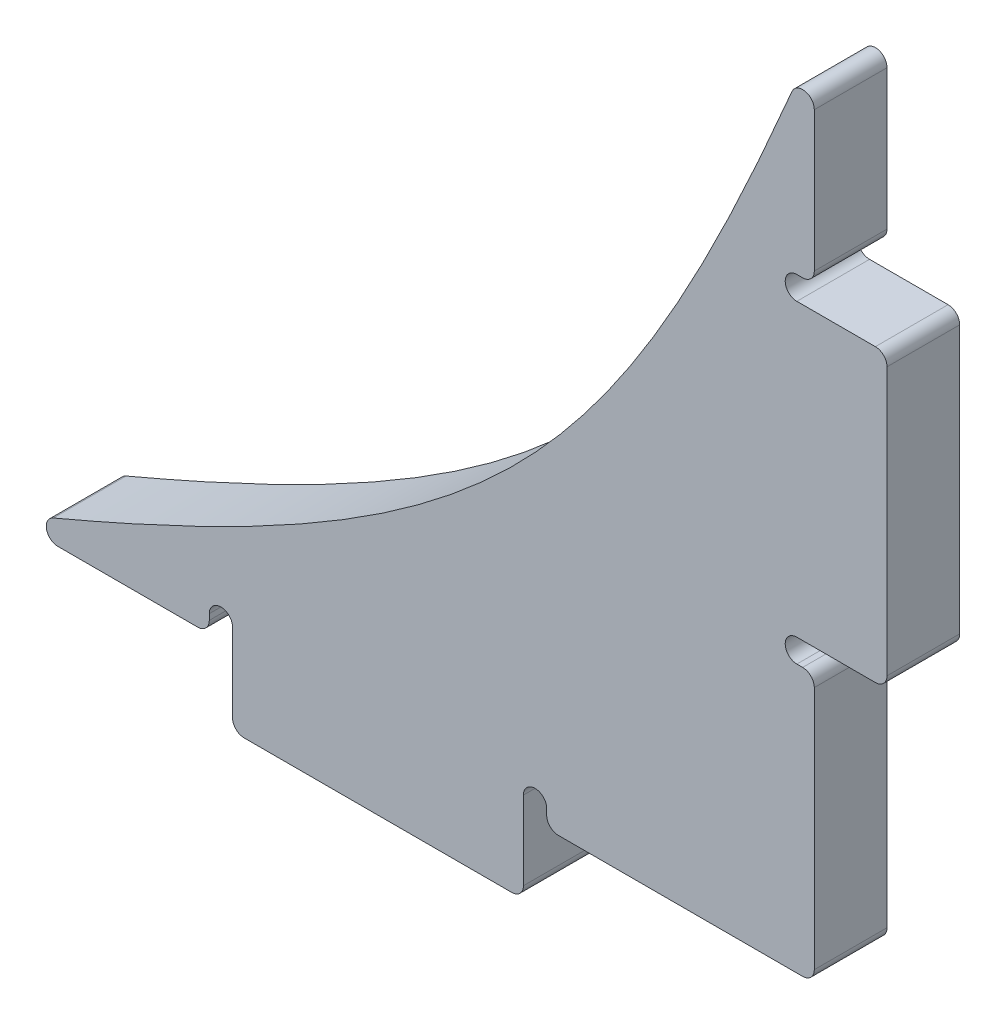
SolidWorks part; units mm, degrees
material "6061-T6 (SS)"
ref_plane "Front Plane" through (0, 0, 0) normal (0, 0, 1) x (1, 0, 0)
ref_plane "Top Plane" through (0, 0, 0) normal (0, 1, 0) x (1, 0, 0)
ref_plane "Right Plane" through (0, 0, 0) normal (1, 0, 0) x (0, 0, -1)
sketch "Sketch1" plane through (0, 0, 0) normal (0, 0, 1) x (1, 0, 0)
  line L0 (22.86, 22.86) -> (14.0603, 1.4879) construction
  line L1 (22.86, -12.7) -> (-12.7, -12.7)
  line L2 (22.86, -12.7) -> (22.86, 22.86)
  line L5 (5.08, 5.08) -> (22.86, -12.7) construction
  line L6 (22.86, 22.86) -> (-12.7, -12.7) construction
  line L7 (14.0603, 1.4879) -> (8.6721, -3.9003) construction
  line L8 (8.6721, -3.9003) -> (-12.7, -12.7) construction
  spline S0 degree 3 poles (22.86, 22.86) (14.0603, 1.4879) (8.6721, -3.9003) (-12.7, -12.7) knots 0 0 0 0 1 1 1 1
  point P0 (0, 0)
  point P9 (11.3662, -1.2062)
  dimension "D1" = 35.56
  dimension "D2" = 35.56
  dimension "D3" = 7.62
  dimension "D4" = 12.7
  dimension "D5" = 17.78
extrude "Boss-Extrude1" add sketch "Sketch1" along normal blind 3.175
sketch "Sketch2" plane through (0, -12.7, 0) normal (0, -1, 0) x (1, 0, 0)
  line L0 (-12.7, 3.175) -> (22.86, 3.175) construction
  line L1 (-2.54, 3.175) -> (10.16, 3.175)
  line L2 (-2.54, 3.175) -> (-2.54, 0)
  line L3 (-2.54, 0) -> (10.16, 0)
  line L4 (10.16, 3.175) -> (10.16, 0)
  line L5 (-12.7, 0) -> (22.86, 0) construction
  line L6 (22.86, 3.175) -> (22.86, 0) construction
  dimension "D1" = 12.7
  dimension "D2" = 12.7
extrude "Boss-Extrude2" add sketch "Sketch2" along normal blind 3.175
sketch "Sketch3" plane through (22.86, 0, 0) normal (1, 0, 0) x (0, 0, -1)
  line L0 (-3.175, -12.7) -> (-3.175, 22.86) construction
  line L1 (-3.175, 0) -> (0, 0)
  line L2 (-3.175, 0) -> (-3.175, 12.7)
  line L3 (-3.175, 12.7) -> (0, 12.7)
  line L4 (0, 0) -> (0, 12.7)
  line L5 (0, -12.7) -> (0, 22.86) construction
  line L6 (-3.175, -12.7) -> (0, -12.7) construction
  dimension "D1" = 12.7
  dimension "D2" = 12.7
extrude "Boss-Extrude3" add sketch "Sketch3" along normal blind 3.175
sketch "Sketch4" plane through (0, 0, 3.175) normal (0, 0, 1) x (1, 0, 0)
  line L0 (-12.7, -12.7) -> (-2.54, -12.7) construction
  line L1 (10.16, -12.7) -> (22.86, -12.7) construction
  line L2 (22.86, -12.7) -> (22.86, 0) construction
  line L3 (22.86, 12.7) -> (22.86, 22.86) construction
  line L4 (-2.54, -15.875) -> (-2.54, -12.7) construction
  line L5 (10.16, -15.875) -> (10.16, -12.7) construction
  line L6 (26.035, 0) -> (22.86, 0) construction
  line L7 (26.035, 12.7) -> (22.86, 12.7) construction
  line L8 (-3.556, -11.938) -> (-3.556, -12.7)
  line L9 (-3.556, -12.7) -> (-2.54, -12.7)
  line L10 (-2.54, -12.7) -> (-2.54, -11.938)
  line L11 (10.16, -11.938) -> (10.16, -12.7)
  line L12 (10.16, -12.7) -> (11.176, -12.7)
  line L13 (11.176, -12.7) -> (11.176, -11.938)
  line L14 (22.098, -1.016) -> (22.86, -1.016)
  line L15 (22.86, -1.016) -> (22.86, 0)
  line L16 (22.86, 0) -> (22.098, 0)
  line L17 (22.098, 12.7) -> (22.86, 12.7)
  line L18 (22.86, 12.7) -> (22.86, 13.716)
  line L19 (22.86, 13.716) -> (22.098, 13.716)
  arc A0 (-2.54, -11.938) -> (-3.556, -11.938) centre (-3.048, -11.938) ccw
  arc A1 (11.176, -11.938) -> (10.16, -11.938) centre (10.668, -11.938) ccw
  arc A2 (22.098, 0) -> (22.098, -1.016) centre (22.098, -0.508) ccw
  arc A3 (22.098, 13.716) -> (22.098, 12.7) centre (22.098, 13.208) ccw
  dimension "D1" = 1.016
  dimension "D2" = 1.016
  dimension "D3" = 1.016
  dimension "D4" = 1.016
  dimension "D5" = 0.762
  dimension "D6" = 0.762
  dimension "D7" = 0.762
  dimension "D8" = 0.762
extrude "Cut-Extrude1" cut sketch "Sketch4" against normal up to next
fillet "Fillet1" radius 0.508 11 edges at (22.86, 13.716, 1.5875) (26.035, 12.7, 1.5875) (26.035, 0, 1.5875) (22.86, -1.016, 1.5875) (22.86, -12.7, 1.5875) (11.176, -12.7, 1.5875) (10.16, -15.875, 1.5875) (-2.54, -15.875, 1.5875) (-3.556, -12.7, 1.5875) (-12.7, -12.7, 1.5875) (22.86, 22.86, 1.5875)
